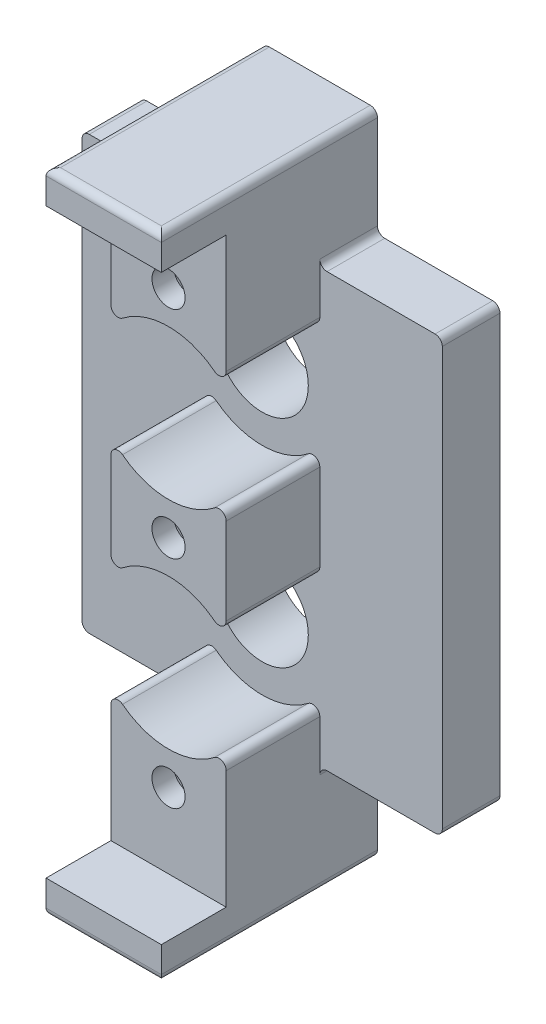
SolidWorks part; units mm, degrees
ref_plane "정면" through (0, 0, 0) normal (0, 0, 1) x (1, 0, 0)
ref_plane "윗면" through (0, 0, 0) normal (0, 1, 0) x (1, 0, 0)
ref_plane "우측면" through (0, 0, 0) normal (1, 0, 0) x (0, 0, -1)
sketch "스케치1" plane through (0, 0, 0) normal (0, 0, 1) x (1, 0, 0)
  line L1 (-12.5, 15) -> (12.5, 15)
  line L2 (-12.5, 15) -> (-12.5, -15)
  line L3 (-12.5, -15) -> (12.5, -15)
  line L4 (12.5, 15) -> (12.5, -15)
  circle A0 centre (0, 7.5) radius 3.2
  circle A1 centre (0, -7.5) radius 3.2
  point P10 (0, 15)
  point P11 (12.5, 0)
  dimension "D3" = 6.4
  dimension "D4" = 6.4
  dimension "D1" = 30
  dimension "D2" = 25
  dimension "D5" = 15
  dimension "D6" = 7.5
extrude "보스-돌출1" add sketch "스케치1" along normal blind 4
sketch "스케치2" plane through (0, 0, 4) normal (0, 0, 1) x (1, 0, 0)
  line L5 (4, 20.2) -> (-4, 20.2)
  line L6 (4, 20.2) -> (4, -20.2)
  line L7 (4, -20.2) -> (-4, -20.2)
  line L8 (-4, 20.2) -> (-4, -20.2)
  circle A0 centre (0, 0) radius 1.15
  circle A1 centre (0, 15) radius 1.15
  circle A2 centre (0, -15) radius 1.15
  point P9 (0, 0)
  point P10 (0, 0)
  point P11 (0, 0)
  point P14 (0, 0)
  point P15 (0, 0)
  dimension "D5" = 2.3
  dimension "D6" = 2.3
  dimension "D7" = 2.3
  dimension "D1" = 8
  dimension "D2" = 4
  dimension "D3" = 15
  dimension "D4" = 15
  dimension "D8" = 5.2
  dimension "D9" = 5.2
sketch "스케치5" plane through (0, 0, 4) normal (0, 0, 1) x (1, 0, 0)
  circle A0 centre (0, 7.5) radius 5.2
  circle A1 centre (0, -7.5) radius 5.2
  circle A2 centre (0, -7.5) radius 3.2 construction
  dimension "D1" = 10.4
extrude "보스-돌출2" add sketch "스케치2" along normal blind 6.5
extrude "컷-돌출1" cut sketch "스케치5" along normal up to surface (6.5 mm away) up to face at (0, 0, 10.5)
sketch "스케치6" plane through (0, 0, 4) normal (0, 0, -1) x (-1, 0, 0)
  line L0 (12.5, -15) -> (-12.5, -15) construction
  line L1 (-4, 20.2) -> (4, 20.2)
  line L2 (-4, 20.2) -> (-4, 15)
  line L3 (-4, 15) -> (4, 15)
  line L4 (4, 20.2) -> (4, 15)
  line L5 (4, -20.2) -> (-4, -20.2)
  line L6 (4, -20.2) -> (4, -15)
  line L7 (4, -15) -> (-4, -15)
  line L8 (-4, -20.2) -> (-4, -15)
  point P13 (-1.6081, -21)
  point P14 (0, 0)
extrude "보스-돌출4" add sketch "스케치6" along normal up to surface (4 mm away) up to face at (0, 0, 0)
sketch "스케치7" plane through (0, 0, 0) normal (0, 0, -1) x (-1, 0, 0)
  line L1 (2.5115, 15) -> (1.2557, 17.175)
  line L2 (1.2557, 17.175) -> (-1.2557, 17.175)
  line L3 (-1.2557, 17.175) -> (-2.5115, 15)
  line L4 (-2.5115, 15) -> (-1.2557, 12.825)
  line L5 (-1.2557, 12.825) -> (1.2557, 12.825)
  line L6 (1.2557, 12.825) -> (2.5115, 15)
  line L7 (2.5115, 0) -> (1.2557, 2.175)
  line L8 (1.2557, 2.175) -> (-1.2557, 2.175)
  line L9 (-1.2557, 2.175) -> (-2.5115, 0)
  line L10 (-2.5115, 0) -> (-1.2557, -2.175)
  line L11 (-1.2557, -2.175) -> (1.2557, -2.175)
  line L12 (1.2557, -2.175) -> (2.5115, 0)
  line L13 (2.5115, -15) -> (1.2557, -12.825)
  line L14 (1.2557, -12.825) -> (-1.2557, -12.825)
  line L15 (-1.2557, -12.825) -> (-2.5115, -15)
  line L16 (-2.5115, -15) -> (-1.2557, -17.175)
  line L17 (-1.2557, -17.175) -> (1.2557, -17.175)
  line L18 (1.2557, -17.175) -> (2.5115, -15)
  circle A0 centre (0, 15) radius 2.175 construction
  circle A1 centre (0, 0) radius 2.175 construction
  circle A2 centre (0, -15) radius 2.175 construction
  point P18 (0, 0)
  point P26 (0, 0)
  point P27 (0, 0)
  point P28 (0, 0)
  point P29 (0, 0)
  dimension "D1" = 4.35
  dimension "D2" = 4.35
  dimension "D3" = 4.35
  dimension "D4" = 15
  dimension "D5" = 15
extrude "컷-돌출2" cut sketch "스케치7" against normal blind 9
sketch "스케치8" plane through (0, 0, 0) normal (0, 0, -1) x (-1, 0, 0)
  line L0 (-4, -20.2) -> (-4, -15) construction
  line L1 (4, 20.2) -> (-4, 20.2)
  line L2 (4, 20.2) -> (4, 22.5)
  line L3 (4, 22.5) -> (-4, 22.5)
  line L4 (-4, 20.2) -> (-4, 22.5)
  line L5 (4, -20.2) -> (-4, -20.2)
  line L6 (4, -20.2) -> (4, -22.5)
  line L7 (4, -22.5) -> (-4, -22.5)
  line L8 (-4, -20.2) -> (-4, -22.5)
  line L9 (-4, 15) -> (-4, 20.2) construction
  dimension "D1" = 45
  dimension "D2" = 22.5
extrude "보스-돌출5" add sketch "스케치8" against normal blind 15
fillet "필렛2" radius 0.5 22 edges at (4, -15, 2) (-4, -15, 2) (-4, 22.5, 7.5) (0, 22.5, 15) (4, 22.5, 7.5) (0, -22.5, 15) (-4, -22.5, 7.5) (4, -22.5, 7.5) (-4, 4.1774, 7.25) (-4, 10.8226, 7.25) (4, 10.8226, 7.25) (4, 4.1774, 7.25) (-12.5, 15, 2) (12.5, 15, 2) (-4, -10.8226, 7.25) (-4, -4.1774, 7.25) (12.5, -15, 2) (4, -4.1774, 7.25) (4, -10.8226, 7.25) (-12.5, -15, 2) (-4, 15, 2) (4, 15, 2)
